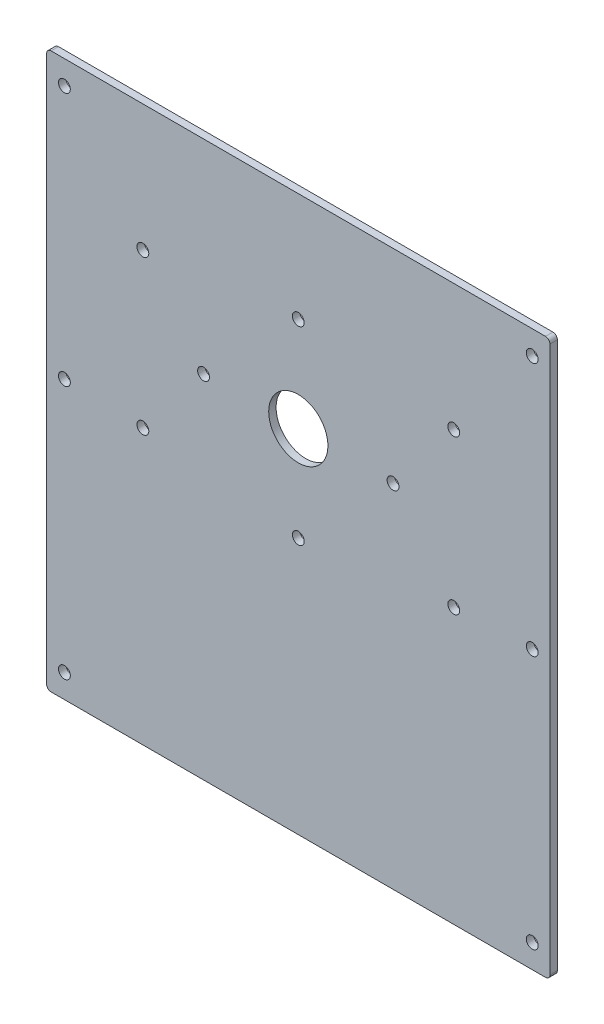
SolidWorks part; units mm, degrees
ref_plane "Front Plane" through (0, 0, 0) normal (0, 0, 1) x (1, 0, 0)
ref_plane "Top Plane" through (0, 0, 0) normal (0, 1, 0) x (1, 0, 0)
ref_plane "Right Plane" through (0, 0, 0) normal (1, 0, 0) x (0, 0, -1)
ref_plane "Plane1" through (0, 0, 5) normal (0, 0, 1) x (1, 0, 0)
sketch "Sketch1" plane through (0, 0, 5) normal (0, 0, 1) x (1, 0, 0)
  line L0 (-170, 184.5) -> (-170, -184.5)
  line L1 (-167, -187.5) -> (167, -187.5)
  line L2 (170, -184.5) -> (170, 184.5)
  line L3 (167, 187.5) -> (-167, 187.5)
  arc A0 (-167, 187.5) -> (-170, 184.5) centre (-167, 184.5) ccw
  arc A1 (-170, -184.5) -> (-167, -187.5) centre (-167, -184.5) ccw
  arc A2 (167, -187.5) -> (170, -184.5) centre (167, -184.5) ccw
  arc A3 (170, 184.5) -> (167, 187.5) centre (167, 184.5) ccw
  circle A4 centre (0, 50) radius 20
  circle A5 centre (-64, 50) radius 4
  circle A6 centre (0, 114) radius 4
  circle A7 centre (64, 50) radius 4
  circle A8 centre (0, -14) radius 4
  circle A9 centre (158, 0) radius 4
  circle A10 centre (-158, 0) radius 4
  circle A11 centre (158, 171.5) radius 4
  circle A12 centre (-158, 171.5) radius 4
  circle A13 centre (-158, -171.5) radius 4
  circle A14 centre (158, -171.5) radius 4
  circle A15 centre (-105, 102) radius 4
  circle A16 centre (-105, -2) radius 4
  circle A17 centre (105, 102) radius 4
  circle A18 centre (105, -2) radius 4
  dimension "D2" = 8
  dimension "D1" = 104
  dimension "D3" = 210
extrude "Boss-Extrude1" add sketch "Sketch1" against normal blind 5
